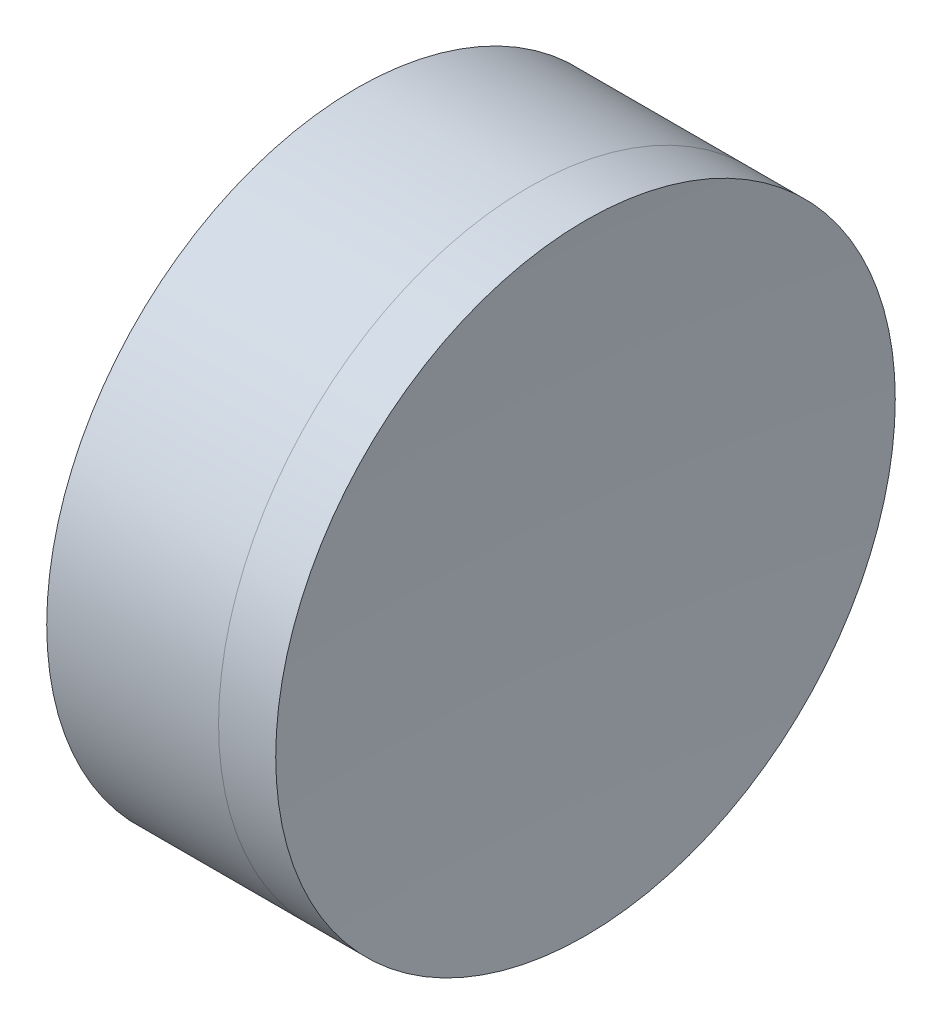
SolidWorks part; units mm, degrees
ref_plane "前视基准面" through (0, 0, 0) normal (0, 0, 1) x (1, 0, 0)
ref_plane "上视基准面" through (0, 0, 0) normal (0, 1, 0) x (1, 0, 0)
ref_plane "右视基准面" through (0, 0, 0) normal (1, 0, 0) x (0, 0, -1)
sketch "草图1" plane through (0, 0, 0) normal (0, 1, 0) x (1, 0, 0)
  line L0 (-0.8161, 0) -> (450.5508, 0) construction
  line L1 (256.4064, 12.7) -> (263.4515, 12.7)
  line L4 (256.4064, -12.7) -> (263.4515, -12.7)
  arc A0 (256.4064, -12.7) -> (256.4064, 12.7) centre (224.8674, 0) ccw
  arc A1 (263.4515, 12.7) -> (263.4515, -12.7) centre (293.3674, 0) ccw
  point P6 (258.8674, 0)
  point P8 (260.8674, 0)
  dimension "D3" = 12.7
  dimension "D4" = 2
  dimension "D1" = 34
  dimension "D5" = 32.5
  dimension "D2" = 12.7
revolve "旋转1" add sketch "草图1" angle 360 about L0
sketch "草图2" plane through (0, 0, 0) normal (0, 1, 0) x (1, 0, 0)
  line L2 (256.4064, 0) -> (272.9951, 0) construction
  line L3 (256.4064, -12.7) -> (256.4064, 12.7) construction
  line L6 (263.4515, 12.7) -> (265.7941, 12.7)
  line L7 (263.4515, -12.7) -> (265.7941, -12.7)
  arc A2 (263.4515, 12.7) -> (263.4515, -12.7) centre (293.3674, 0) ccw construction
  arc A3 (263.4515, 12.7) -> (263.4515, -12.7) centre (293.3674, 0) ccw
  arc A4 (265.7941, 12.7) -> (265.7941, -12.7) centre (454.5674, 0) ccw
  point P8 (260.8674, 0)
  point P9 (265.3674, 0)
  dimension "D1" = 4.5
  dimension "D2" = 189.2
revolve "旋转3" add sketch "草图2" angle 360 about L2
